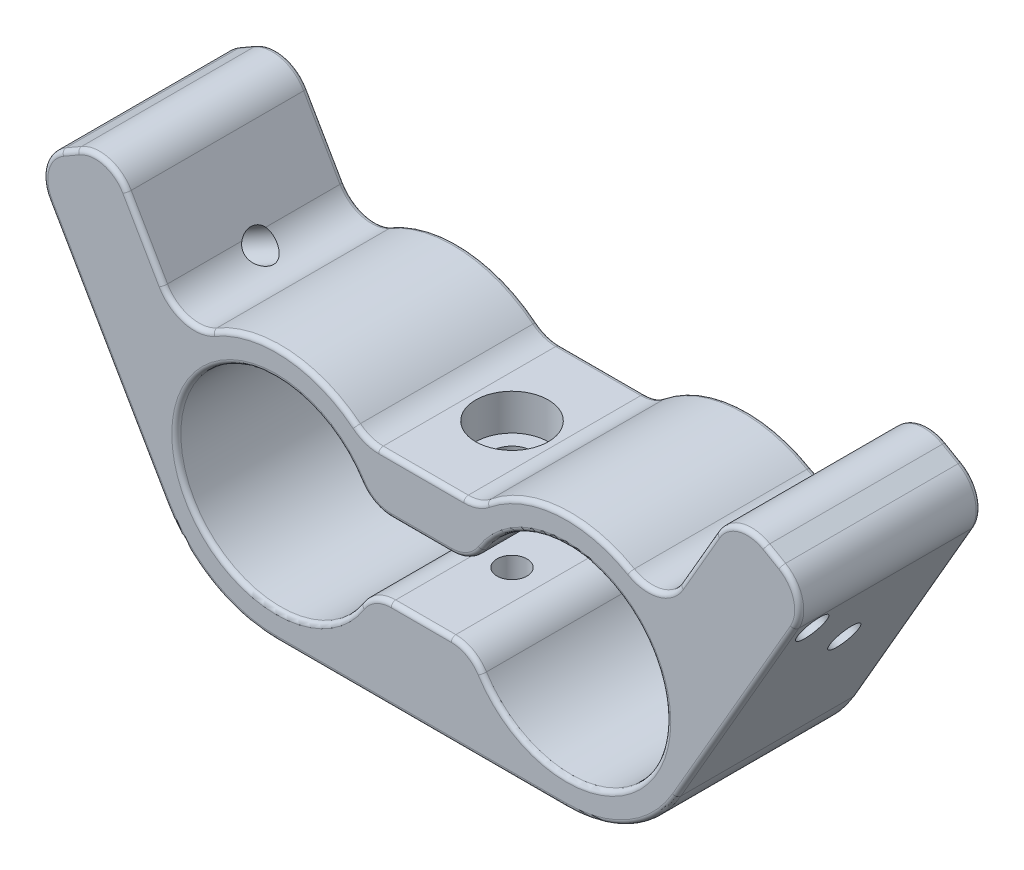
SolidWorks part; units mm, degrees
material "Сплав 2024"
ref_plane "Спереди" through (0, 0, 0) normal (0, 0, 1) x (1, 0, 0)
ref_plane "Сверху" through (0, 0, 0) normal (0, 1, 0) x (1, 0, 0)
ref_plane "Справа" through (0, 0, 0) normal (1, 0, 0) x (0, 0, -1)
sketch "Эскиз1" plane through (0, 0, 0) normal (0, 0, 1) x (1, 0, 0)
  line L0 (-97.2999, 0) -> (107.2229, 0) construction
  line L1 (0, 45.7486) -> (0, -47.2091) construction
  line L2 (-6.202, 10) -> (6.202, 10)
  line L3 (-5.753, 4) -> (5.753, 4)
  line L4 (43.1244, 18.9808) -> (28.1244, -7)
  line L5 (-43.1244, 18.9808) -> (-28.1244, -7)
  line L6 (-34.4641, 23.9808) -> (-26.1723, 9.619)
  line L7 (34.4641, 23.9808) -> (26.1723, 9.619)
  line L8 (-43.1244, 18.9808) -> (-34.4641, 23.9808)
  line L9 (34.4641, 23.9808) -> (43.1244, 18.9808)
  line L10 (-16, -14) -> (16, -14)
  line L11 (-5.753, -4) -> (5.753, -4)
  arc A0 (-5.753, 4) -> (-5.753, -4) centre (-16, 0) ccw
  arc A1 (5.753, -4) -> (5.753, 4) centre (16, 0) ccw
  arc A2 (-6.202, 10) -> (-26.1723, 9.619) centre (-16, 0) ccw
  arc A3 (-28.1244, -7) -> (-16, -14) centre (-16, 0) ccw
  arc A4 (16, -14) -> (28.1244, -7) centre (16, 0) ccw
  circle A5 centre (-16, 0) radius 14 construction
  arc A6 (26.1723, 9.619) -> (6.202, 10) centre (16, 0) ccw
  circle A7 centre (-16, 0) radius 11 construction
  point P8 (30, 0)
  point P10 (-5.4806, 3.2161)
  point P29 (-2, 0)
  point P36 (26.5194, 3.2161)
  dimension "D1" = 22
  dimension "D2" = 22
  dimension "D6" = 3
  dimension "D3" = 16
  dimension "D4" = 16
  dimension "D7" = 6
  dimension "D8" = 30
  dimension "D9" = 30
  dimension "D10" = 10
  dimension "D11" = 10
  dimension "D12" = 10
  dimension "D13" = 8
  dimension "D14" = 30
  dimension "D15" = 30
  dimension "D5" = 3
extrude "Бобышка-Вытянуть2" add sketch "Эскиз1" along normal blind 20
sketch "Эскиз3" plane through (0, 10, 0) normal (0, 1, 0) x (1, 0, 0)
  line L0 (0, 0) -> (0, -20) construction
  line L1 (6.202, -20) -> (-6.202, -20) construction
  line L2 (6.202, -10) -> (-6.202, -10) construction
  line L3 (6.202, -20) -> (6.202, 0) construction
  line L4 (-6.202, -20) -> (-6.202, 0) construction
hole_wizard "Цековка для винта с внутренним шестигранником M41" positions "Эскиз5" profile "Эскиз4" counterbore size "M4" standard "Ansi Metric" end condition up to next
sketch "Эскиз5" plane through (0, 10, 0) normal (0, 1, 0) x (1, 0, 0)
  line L0 (0, 0) -> (0, -20) construction
  point P0 (0, -10)
sketch "Эскиз4" plane through (0, 10, 10) normal (1, 0, 0) x (0, 0, 1)
  line L0 (0, 0) -> (0, 6)
  line L1 (0, 6) -> (2.25, 6)
  line L3 (2.25, 6) -> (2.25, 4)
  line L4 (2.25, 4) -> (4, 4)
  line L5 (4, 4) -> (4, 0)
  line L7 (4, 0) -> (0, 0)
  line L11 (0, -6.35) -> (0, 107.95) construction
  dimension "Диаметр сквозного отверстия" = 4.5
  dimension "Глубина сквозного отверстия" = 6
  dimension "Диаметр цековки" = 8
  dimension "Глубина цековки" = 4
hole_wizard "Отверстие обработанное метчиком M4x0.71" positions "Эскиз7" profile "Эскиз6" tap size "M4x0.7" standard "Ansi Metric" end condition through all
sketch "Эскиз7" plane through (0, -4, 0) normal (0, 1, 0) x (1, 0, 0)
  line L0 (0, 0) -> (0, -20) construction
  point P0 (0, -10)
sketch "Эскиз6" plane through (0, -4, 10) normal (1, 0, 0) x (0, 0, 1)
  line L0 (0, 0) -> (0, 10)
  line L1 (0, 10) -> (1.65, 10)
  line L2 (1.65, 10) -> (1.65, 0)
  line L5 (1.65, 0) -> (0, 0)
  line L11 (0, -6.35) -> (0, 107.95) construction
  dimension "Диаметр проходного сверла" = 3.3
  dimension "Глубина проходного сверла" = 10
cosmetic thread "Отверстие резьбы1" parameters "D2"=4
fillet "Скругление1" radius 4 12 edges at (-5.753, -4, 10) (5.753, -4, 10) (5.753, 4, 10) (-5.753, 4, 10) (-43.1244, 18.9808, 10) (-34.4641, 23.9808, 10) (43.1244, 18.9808, 10) (34.4641, 23.9808, 10) (26.1723, 9.619, 10) (6.202, 10, 10) (-6.202, 10, 10) (-26.1723, 9.619, 10)
fillet "Скругление2" radius 0.5 56 edges at (14.9086, 13.9574, 0) (6.0196, 10.2288, 0) (0, 10, 0) (-6.0196, 10.2288, 0) (-14.9086, 13.9574, 0) (-26.0353, 11.7248, 0) (-30.4641, 17.0526, 0) (-34.8929, 22.3804, 0) (-38.7942, 21.4808, 0) (-41.524, 18.5519, 0) (-34.6244, 4.2583, 0) (-23, -12.1244, 0) (0, -14, 0) (23, -12.1244, 0) (34.6244, 4.2583, 0) (41.524, 18.5519, 0) (38.7942, 21.4808, 0) (34.8929, 22.3804, 0) (30.4641, 17.0526, 0) (5.2436, -4.4976, 0) (0, -4, 0) (-5.2436, -4.4976, 0) (-27, 0, 0) (-5.2436, 4.4976, 0) (0, 4, 0) (5.2436, 4.4976, 0) (-5.2436, 4.4976, 20) (0, 4, 20) (5.2436, 4.4976, 20) (27, 0, 20) (5.2436, -4.4976, 20) (0, -4, 20) (-5.2436, -4.4976, 20) (34.8929, 22.3804, 20) (38.7942, 21.4808, 20) (41.524, 18.5519, 20) (34.6244, 4.2583, 20) (23, -12.1244, 20) (0, -14, 20) (-23, -12.1244, 20) (-34.6244, 4.2583, 20) (-41.524, 18.5519, 20) (-38.7942, 21.4808, 20) (-34.8929, 22.3804, 20) (-30.4641, 17.0526, 20) (-26.0353, 11.7248, 20) (-14.9086, 13.9574, 20) (-6.0196, 10.2288, 20) (0, 10, 20) (6.0196, 10.2288, 20) (14.9086, 13.9574, 20) (26.0353, 11.7248, 20) (26.0353, 11.7248, 0) (27, 0, 0) (-27, 0, 20) (30.4641, 17.0526, 20)
sketch "Эскиз8" plane through (24.1244, -13.9282, 0) normal (0.866, -0.5, 0) x (0, 0, -1)
  line L0 (-10, 34) -> (-10, 8) construction
  line L1 (-0.5, 34) -> (-19.5, 34) construction
  line L2 (-19.5, 8) -> (-0.5, 8) construction
  line L3 (-19.5, 25) -> (-0.5, 25) construction
  line L4 (-19.5, 34) -> (-19.5, 8) construction
  line L5 (-0.5, 8) -> (-0.5, 34) construction
  line L6 (-19.5, 38) -> (-0.5, 38) construction
  dimension "D1" = 13
hole_wizard "Отверстие обработанное метчиком M4x0.72" positions "Эскиз10" profile "Эскиз9" tap size "M4x0.7" standard "Ansi Metric" end condition through all
sketch "Эскиз10" plane through (24.1244, -13.9282, 0) normal (0.866, -0.5, 0) x (-0.5, -0.866, 0)
  line L0 (-25, -19.5) -> (-25, -0.5) construction
  point P0 (-25, -10)
sketch "Эскиз9" plane through (36.6244, 7.7224, 10) normal (0, 0, 1) x (0.5, 0.866, 0)
  line L0 (0, 0) -> (0, 75.1936)
  line L1 (0, 75.1936) -> (1.65, 75.1936)
  line L2 (1.65, 75.1936) -> (1.65, 0)
  line L5 (1.65, 0) -> (0, 0)
  line L11 (0, -6.35) -> (0, 107.95) construction
  dimension "Диаметр проходного сверла" = 3.3
  dimension "Глубина проходного сверла" = 75.1936
cosmetic thread "Отверстие резьбы2" parameters "D2"=4
ref_plane "Плоскость1" through (0, 0, 0) normal (1, 0, 0) x (0, 0, -1)
mirror "Зеркальное отражение1" about plane through (0, 0, 0) normal (1, 0, 0) of "Отверстие обработанное метчиком M4x0.72"
sketch "Эскиз11" [suppressed] plane through (-17.8995, -17.8995, 0) normal (-0.7071, -0.7071, 0) x (0, 0, 1)
  line L0 (10, 28.3137) -> (22.9622, 41.2759) construction
  line L1 (19.5, 11.3137) -> (19.5, 42.3137) construction
  circle A0 centre (17.0711, 35.3848) radius 2
  dimension "D2" = 4
  dimension "D1" = 45
  dimension "D3" = 10
extrude "Бобышка-Вытянуть3" [suppressed] add sketch "Эскиз11" along normal blind 8
mirror "Зеркальное отражение2" [suppressed] about plane through (0, 0, 0) normal (1, 0, 0)
sketch "Эскиз12" plane through (-24.1244, -13.9282, 0) normal (-0.866, -0.5, 0) x (0, 0, 1)
  line L0 (10, 25) -> (28.4708, 43.4708) construction
  line L1 (19.5, 8) -> (19.5, 34) construction
  point P5 (17.0711, 32.0711)
  dimension "D1" = 45
  dimension "D2" = 10
hole_wizard "Отверстие обработанное метчиком M4x0.73" positions "Эскиз14" profile "Эскиз13" tap size "M4x0.7" standard "Ansi Metric"
sketch "Эскиз14" plane through (-24.1244, -13.9282, 0) normal (-0.866, -0.5, 0) x (-0.5, 0.866, 0)
  point P0 (32.0711, -17.0711)
sketch "Эскиз13" plane through (-40.1599, 13.8462, 17.0711) normal (0, 0, 1) x (0.5, -0.866, 0)
  line L0 (0, 0) -> (0, 4.9914)
  line L1 (0, 4.9914) -> (1.65, 4)
  line L2 (1.65, 4) -> (1.65, 0)
  line L5 (1.65, 0) -> (0, 0)
  line L10 (0, 4.9914) -> (-1.65, 4) construction
  line L11 (0, -6.35) -> (0, 107.95) construction
  dimension "Диаметр сверла" = 3.3
  dimension "Глубина сверла" = 4
  dimension "Угол заточки сверла" = 118
cosmetic thread "Отверстие резьбы3" parameters "D1"=6, "D2"=4
mirror "Зеркальное отражение3" about plane through (0, 0, 0) normal (1, 0, 0) of "Отверстие обработанное метчиком M4x0.73"
equation "\"D2@Эскиз1\"=\"D1@Эскиз1\""
equation "\"D4@Эскиз1\"=\"D3@Эскиз1\""
